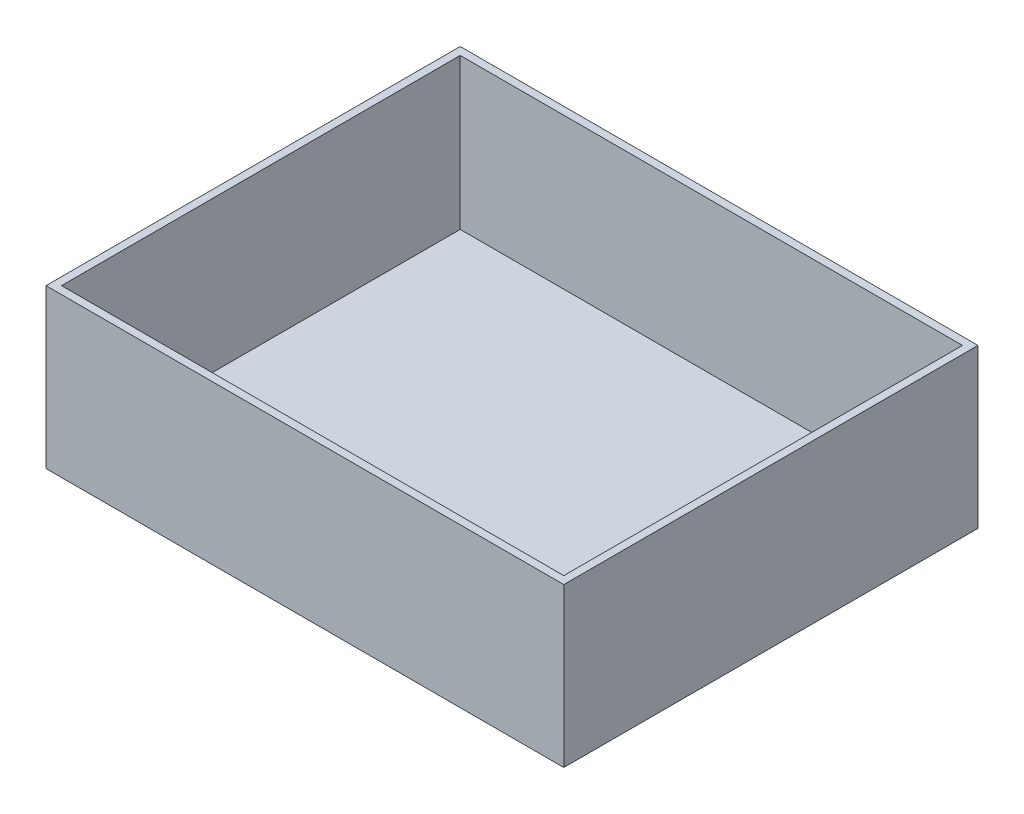
SolidWorks part; units mm, degrees
ref_plane "Front Plane" through (0, 0, 0) normal (0, 0, 1) x (1, 0, 0)
ref_plane "Top Plane" through (0, 0, 0) normal (0, 1, 0) x (1, 0, 0)
ref_plane "Right Plane" through (0, 0, 0) normal (1, 0, 0) x (0, 0, -1)
sketch "Sketch1" plane through (0, 0, 0) normal (0, 1, 0) x (1, 0, 0)
  line L1 (-250, 200) -> (250, 200)
  line L2 (-250, 200) -> (-250, -200)
  line L3 (-250, -200) -> (250, -200)
  line L4 (250, 200) -> (250, -200)
  line L5 (-250, 200) -> (250, -200) construction
  line L6 (-250, -200) -> (250, 200) construction
  point P0 (0, 0)
  point P5 (0, 0)
  dimension "D1" = 400
  dimension "D2" = 500
extrude "Boss-Extrude1" add sketch "Sketch1" along normal blind 153
shell "Shell1" thickness 7.5
